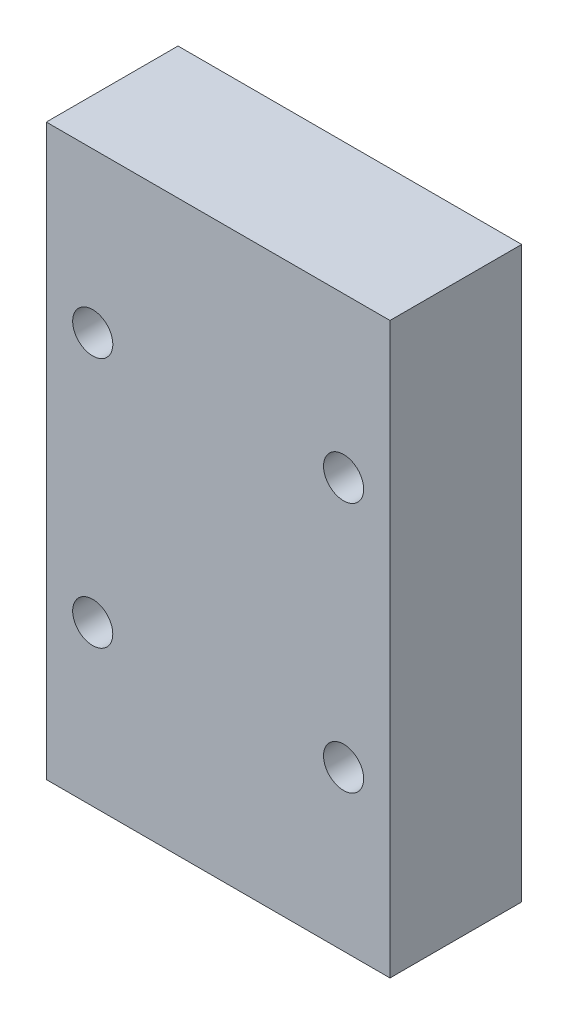
SolidWorks part; units mm, degrees
ref_plane "Front Plane" through (0, 0, 0) normal (0, 0, 1) x (1, 0, 0)
ref_plane "Top Plane" through (0, 0, 0) normal (0, 1, 0) x (1, 0, 0)
ref_plane "Right Plane" through (0, 0, 0) normal (1, 0, 0) x (0, 0, -1)
sketch "Sketch1" plane through (0, 0, 0) normal (0, 0, 1) x (1, 0, 0)
  line L0 (440.4618, -60.8059) -> (426.7618, -60.8059) construction
  line L1 (454.1618, -83.5059) -> (426.7618, -83.5059)
  line L3 (454.1618, -38.1059) -> (426.7618, -38.1059)
  line L5 (454.1618, -83.5059) -> (426.7618, -38.1059) construction
  line L6 (454.1618, -38.1059) -> (426.7618, -83.5059) construction
  line L7 (440.4618, -60.8059) -> (440.4618, -83.5059) construction
  line L8 (426.7618, -83.5059) -> (426.7618, -38.1059)
  line L9 (454.1618, -83.5059) -> (454.1618, -38.1059)
  circle A0 centre (430.4618, -70.8059) radius 1.6
  circle A1 centre (430.4618, -50.8059) radius 1.6
  circle A2 centre (450.4618, -50.8059) radius 1.6
  circle A3 centre (450.4618, -70.8059) radius 1.6
  point P0 (440.4618, -60.8059)
  point P8 (0, 0)
  point P16 (0, 0)
  dimension "D5" = 3.2
  dimension "D6" = 10
  dimension "D1" = 27.4
  dimension "D2" = 45.4
  dimension "D3" = 10
  dimension "D4" = 10
extrude "Boss-Extrude1" add sketch "Sketch1" along normal blind 5 and the other way blind 5.5
